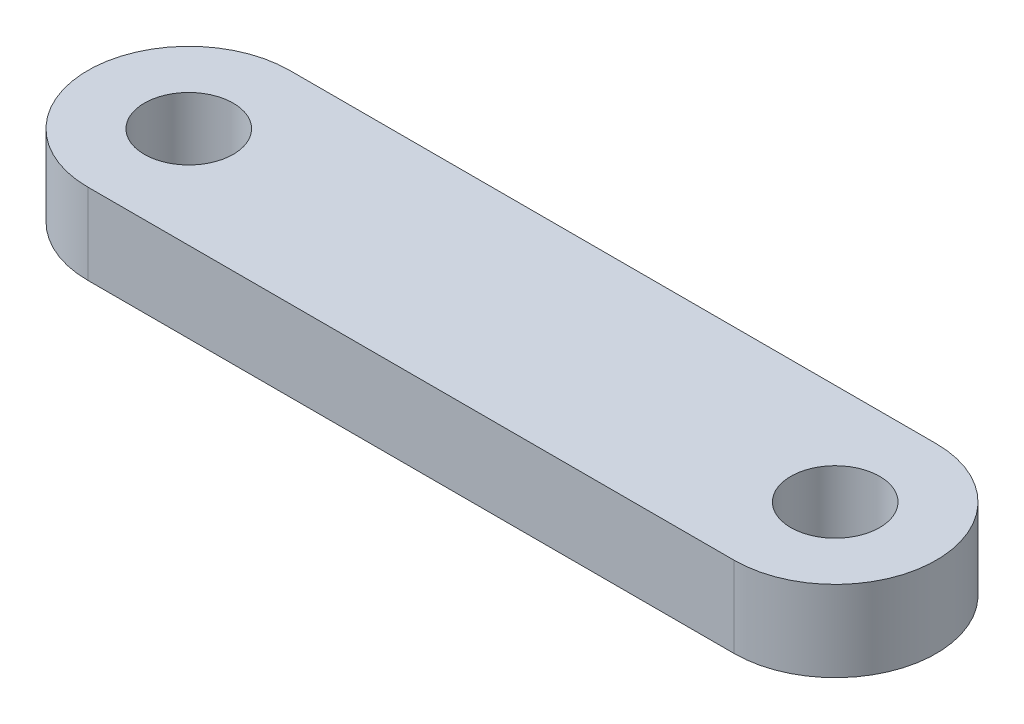
SolidWorks part; units mm, degrees
ref_plane "Front Plane" through (0, 0, 0) normal (0, 0, 1) x (1, 0, 0)
ref_plane "Top Plane" through (0, 0, 0) normal (0, 1, 0) x (1, 0, 0)
ref_plane "Right Plane" through (0, 0, 0) normal (1, 0, 0) x (0, 0, -1)
sketch "Sketch1" plane through (0, 0, 0) normal (0, 1, 0) x (1, 0, 0)
  line L0 (0, 0) -> (16, 0) construction
  line L2 (0, 2.5) -> (16, 2.5)
  line L3 (0, -2.5) -> (16, -2.5)
  arc A0 (0, 2.5) -> (0, -2.5) centre (0, 0) ccw
  arc A1 (16, -2.5) -> (16, 2.5) centre (16, 0) ccw
  circle A2 centre (0, 0) radius 1.1
  circle A3 centre (16, 0) radius 1.1
  point P5 (8, 0)
  dimension "D1" = 2.2
  dimension "D2" = 2.2
extrude "Boss-Extrude1" add sketch "Sketch1" along normal blind 2
